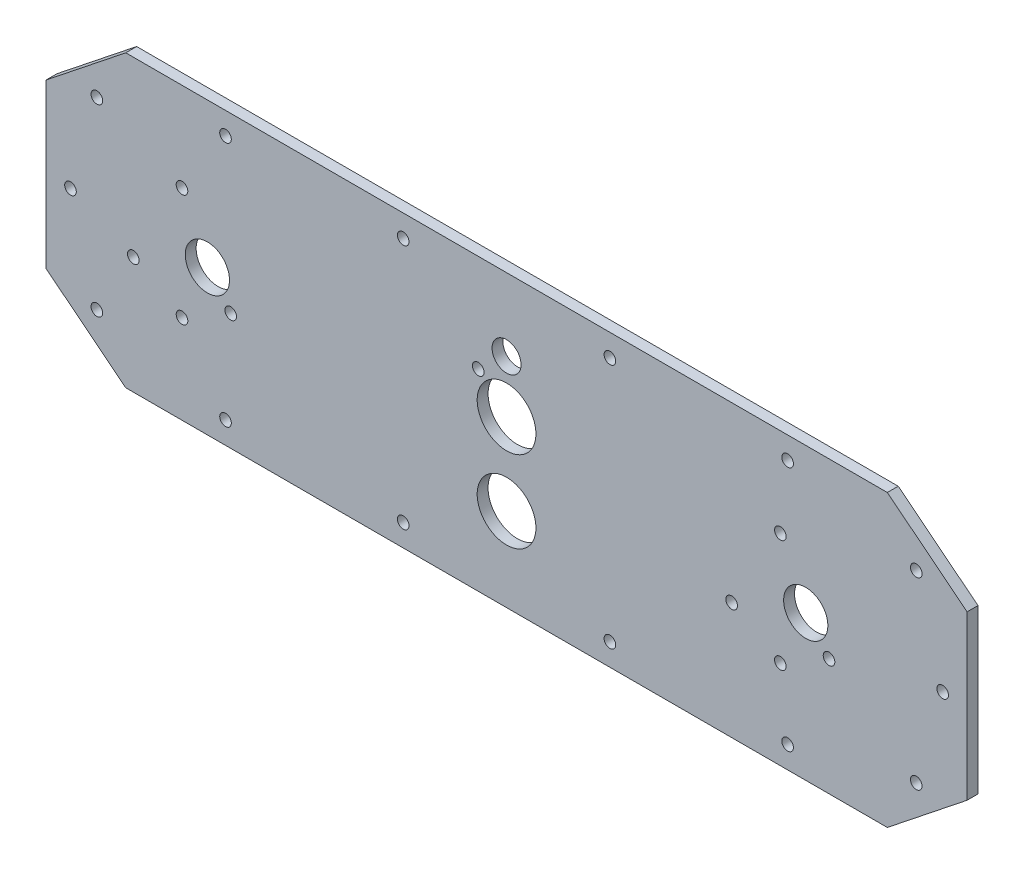
SolidWorks part; units mm, degrees
ref_plane "Alzado" through (0, 0, 0) normal (0, 0, 1) x (1, 0, 0)
ref_plane "Planta" through (0, 0, 0) normal (0, 1, 0) x (1, 0, 0)
ref_plane "Vista lateral" through (0, 0, 0) normal (1, 0, 0) x (0, 0, -1)
sketch "Croquis1" plane through (0, 0, 0) normal (0, 0, 1) x (1, 0, 0)
  line L0 (-127, 22.5) -> (-105, 40)
  line L1 (127, -40) -> (-127, -40) construction
  line L2 (127, -40) -> (127, 40) construction
  line L3 (127, 40) -> (-127, 40) construction
  line L4 (-127, -40) -> (-127, 40) construction
  line L5 (127, -40) -> (-127, 40) construction
  line L6 (127, 40) -> (-127, -40) construction
  line L7 (-105, 40) -> (105, 40)
  line L8 (105, 40) -> (127, 22.5)
  line L9 (127, 22.5) -> (127, -22.5)
  line L10 (127, -22.5) -> (105, -40)
  line L11 (105, -40) -> (-105, -40)
  line L12 (-105, -40) -> (-127, -22.5)
  line L13 (-127, -22.5) -> (-127, 22.5)
  line L14 (0, -40) -> (0, 40) construction
  line L15 (0, 33.9) -> (-28.5, 33.9) construction
  line L16 (-28.5, 33.9) -> (-77.5, 33.9) construction
  line L17 (0, 33.9) -> (28.5, 33.9) construction
  line L18 (28.5, 33.9) -> (77.5, 33.9) construction
  line L19 (0, -33.9) -> (-28.5, -33.9) construction
  line L20 (-28.5, -33.9) -> (-77.5, -33.9) construction
  line L21 (0, -33.9) -> (28.5, -33.9) construction
  line L22 (28.5, -33.9) -> (77.5, -33.9) construction
  line L23 (-127, 0) -> (-120.25, 0) construction
  line L24 (127, 0) -> (120.25, 0) construction
  line L25 (0, 0) -> (-82.5, 0) construction
  line L26 (-112.98, -25.35) -> (112.98, -25.35) construction
  line L27 (-112.98, -25.35) -> (-112.98, 25.35) construction
  line L28 (-112.98, 25.35) -> (112.98, 25.35) construction
  line L29 (112.98, -25.35) -> (112.98, 25.35) construction
  line L30 (-112.98, -25.35) -> (112.98, 25.35) construction
  line L31 (-112.98, 25.35) -> (112.98, -25.35) construction
  line L32 (0, 0) -> (82.5, 0) construction
  line L33 (88.9234, -7.75) -> (75.5, 0) construction
  line L34 (75.5, 0) -> (62.0766, -7.75) construction
  line L35 (-82.5, 0) -> (-89.5, 0) construction
  line L36 (-76.0766, -7.75) -> (-89.5, 0) construction
  line L37 (-89.5, 0) -> (-102.9234, -7.75) construction
  circle A0 centre (0, 20) radius 4
  circle A1 centre (112.98, 25.35) radius 1.6
  circle A2 centre (120.25, 0) radius 1.6
  circle A3 centre (112.98, -25.35) radius 1.6
  circle A4 centre (77.5, -33.9) radius 1.6
  circle A5 centre (28.5, -33.9) radius 1.6
  circle A6 centre (-28.5, -33.9) radius 1.6
  circle A7 centre (-77.5, -33.9) radius 1.6
  circle A8 centre (-112.98, -25.35) radius 1.6
  circle A9 centre (-120.25, 0) radius 1.6
  circle A10 centre (-112.98, 25.35) radius 1.6
  circle A11 centre (-77.5, 33.9) radius 1.6
  circle A12 centre (-28.5, 33.9) radius 1.6
  circle A13 centre (28.5, 33.9) radius 1.6
  circle A14 centre (77.5, 33.9) radius 1.6
  circle A15 centre (-82.5, 0) radius 6.1
  circle A16 centre (82.5, 0) radius 6.1
  circle A17 centre (0, 5.55) radius 8.1
  circle A18 centre (0, -16.95) radius 8.1
  circle A19 centre (-7.8, 13.1) radius 1.6
  circle A20 centre (75.5, 0) radius 15.5 construction
  circle A21 centre (75.5, 15.5) radius 1.6
  circle A22 centre (75.5, -15.5) radius 1.6
  circle A23 centre (62.0766, -7.75) radius 1.6
  circle A24 centre (88.9234, -7.75) radius 1.6
  circle A25 centre (-89.5, 0) radius 15.5 construction
  circle A26 centre (-89.5, 15.5) radius 1.6
  circle A27 centre (-102.9234, -7.75) radius 1.6
  circle A28 centre (-76.0766, -7.75) radius 1.6
  circle A29 centre (-89.5, -15.5) radius 1.6
  point P0 (0, 0)
  point P34 (0, 0)
  dimension "D10" = 8
  dimension "D19" = 3.2
  dimension "D21" = 12.2
  dimension "D23" = 16.2
  dimension "D27" = 3.2
  dimension "D28" = 31
  dimension "D31" = 3.2
  dimension "D32" = 31
  dimension "D1" = 254
  dimension "D2" = 80
  dimension "D3" = 22
  dimension "D4" = 22
  dimension "D5" = 22
  dimension "D6" = 22
  dimension "D7" = 17.5
  dimension "D8" = 17.5
  dimension "D9" = 17.5
  dimension "D11" = 20
  dimension "D12" = 57
  dimension "D13" = 6.1
  dimension "D14" = 6.1
  dimension "D15" = 49
  dimension "D16" = 6.75
  dimension "D17" = 7.98
  dimension "D18" = 2.85
  dimension "D20" = 165
  dimension "D22" = 22.5
  dimension "D24" = 14.45
  dimension "D25" = 7.8
  dimension "D26" = 7.55
  dimension "D29" = 7
  dimension "D30" = 240
  dimension "D33" = 7
  dimension "D34" = 240
extrude "Saliente-Extruir1" add sketch "Croquis1" along normal blind 3
